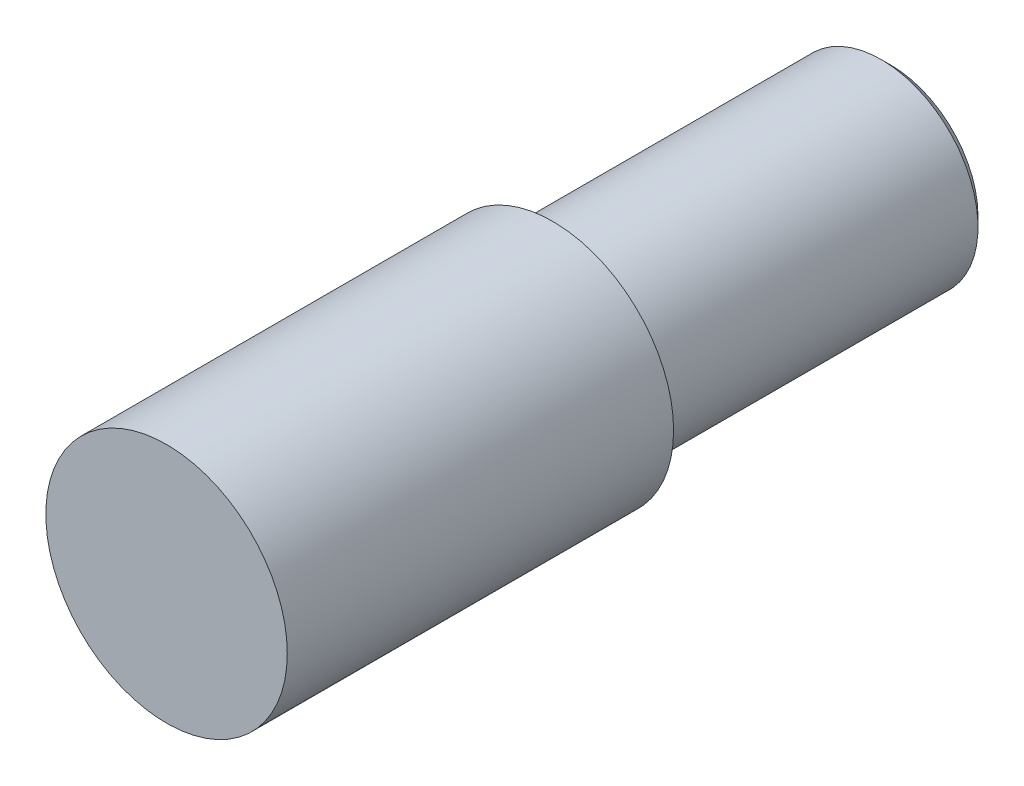
SolidWorks part; units mm, degrees
ref_plane "Front Plane" through (0, 0, 0) normal (0, 0, 1) x (1, 0, 0)
ref_plane "Top Plane" through (0, 0, 0) normal (0, 1, 0) x (1, 0, 0)
ref_plane "Right Plane" through (0, 0, 0) normal (1, 0, 0) x (0, 0, -1)
sketch "Sketch1" plane through (0, 0, 0) normal (0, 0, 1) x (1, 0, 0)
  circle A0 centre (0, 0) radius 12.5
  dimension "D1" = 25
extrude "Boss-Extrude1" add sketch "Sketch1" against normal blind 40
sketch "Sketch2" plane through (0, 0, -40) normal (0, 0, -1) x (-1, 0, 0)
  circle A0 centre (0, 0) radius 10.02
  dimension "D1" = 20.04
extrude "Boss-Extrude2" add sketch "Sketch2" along normal blind 35
chamfer "Chamfer1" distance 1 angle 45 1 edges at (-10.02, 0, -75)
